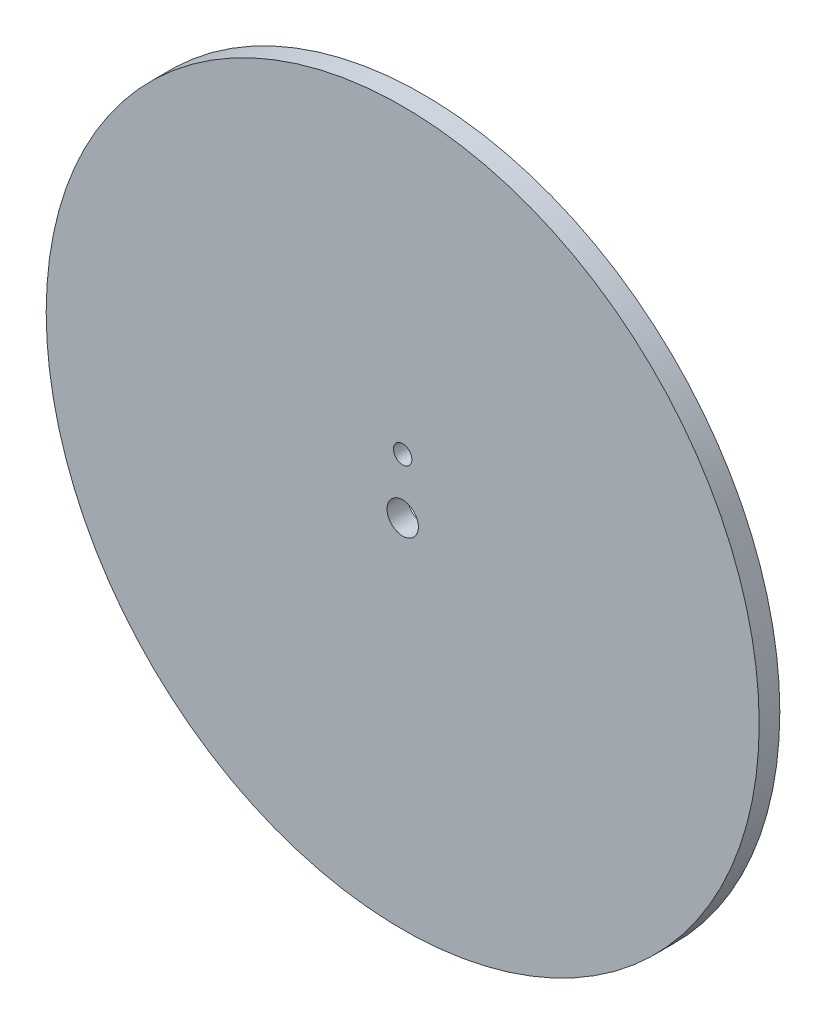
SolidWorks part; units mm, degrees
material "Maple"
ref_plane "Front Plane" through (0, 0, 0) normal (0, 0, 1) x (1, 0, 0)
ref_plane "Top Plane" through (0, 0, 0) normal (0, 1, 0) x (1, 0, 0)
ref_plane "Right Plane" through (0, 0, 0) normal (1, 0, 0) x (0, 0, -1)
sketch "Sketch1" plane through (0, 0, 0) normal (0, 0, 1) x (1, 0, 0)
  line L0 (0, 0) -> (0, 8.5) construction
  circle A0 centre (0, 0) radius 54.915
  circle A1 centre (0, 0) radius 2.415
  circle A2 centre (0, 8.5) radius 1.415
  dimension "D1" = 109.83
  dimension "D2" = 4.83
  dimension "D3" = 2.83
  dimension "D4" = 8.5
extrude "Boss-Extrude1" add sketch "Sketch1" along normal blind 3.175
equation "\"diameter\"=109.83"
equation "\"D1@Sketch1\"=\"diameter\""
equation "\"innerHoleDiameter\"=4.83"
equation "\"D2@Sketch1\"=\"innerHoleDiameter\""
equation "\"screwHoleDiameter\"=2.83"
equation "\"D3@Sketch1\"=\"screwHoleDiameter\""
equation "\"distance\"=8.5"
equation "\"D4@Sketch1\"=\"distance\""
